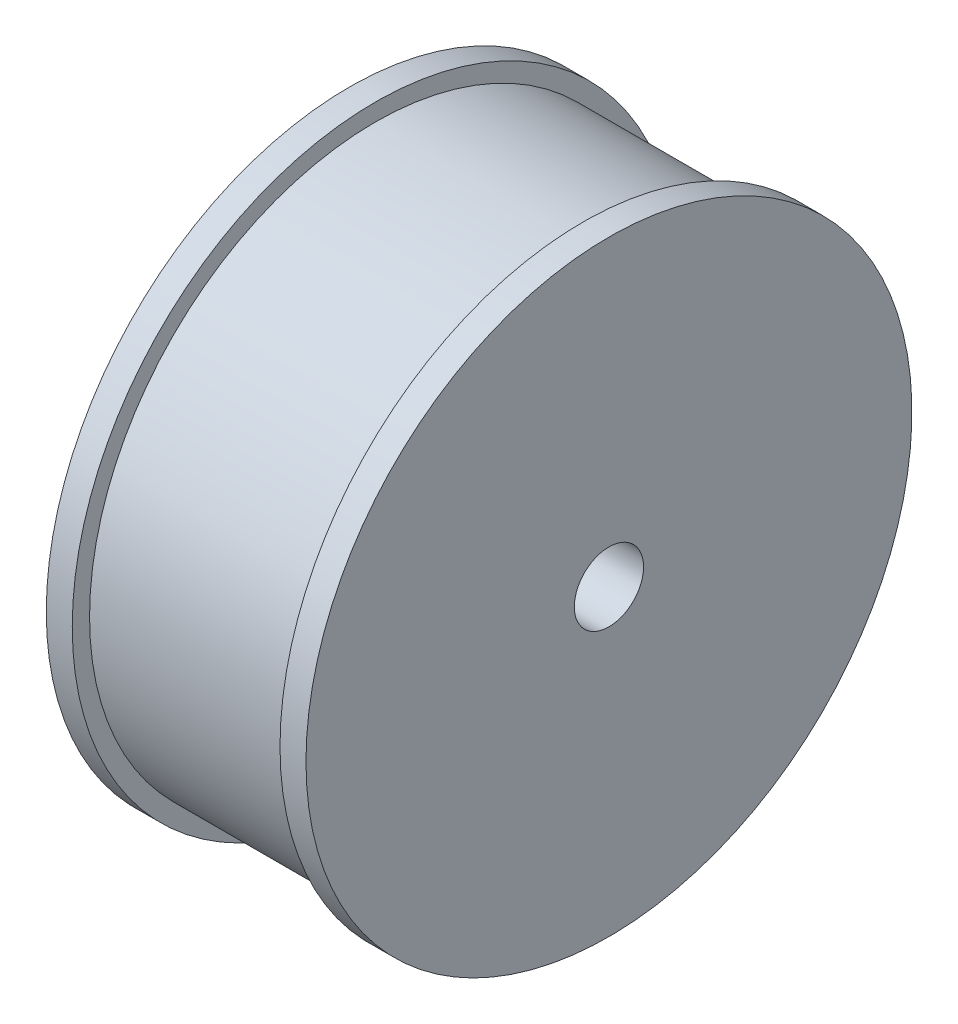
SolidWorks part; units mm, degrees
ref_plane "Front" through (0, 0, 0) normal (0, 0, 1) x (1, 0, 0)
ref_plane "Top" through (0, 0, 0) normal (0, 1, 0) x (1, 0, 0)
ref_plane "Right" through (0, 0, 0) normal (1, 0, 0) x (0, 0, -1)
sketch "Sketch1" plane through (0, 0, 0) normal (0, 0, 1) x (1, 0, 0)
  line L1 (-15, 0) -> (15, 0) construction
  line L2 (12, 35) -> (15, 35)
  line L3 (15, 0) -> (15, 35)
  line L6 (12, 35) -> (12, 33)
  line L7 (-12, 33) -> (12, 33)
  line L8 (0, -50) -> (0, 50) construction
  line L9 (-15, 0) -> (-15, 35)
  line L10 (-12, 35) -> (-15, 35)
  line L11 (-12, 35) -> (-12, 33)
  line L12 (-15, 0) -> (15, 0)
  point P6 (0, 0)
  point P9 (0, 0)
  dimension "D1" = 15
  dimension "D2" = 35
  dimension "D3" = 3
  dimension "D4" = 2
revolve "Revolve1" add sketch "Sketch1" angle 360 about L1
sketch "Sketch4" plane through (-15, 0, 0) normal (-1, 0, 0) x (0, 0, 1)
  circle A0 centre (0, 0) radius 10
  dimension "D1" = 20
extrude "Boss-Extrude2" add sketch "Sketch4" along normal blind 8
sketch "Sketch6" plane through (15, 0, 0) normal (1, 0, 0) x (0, 0, -1)
  circle A0 centre (0, 0) radius 4
  dimension "D1" = 8
extrude "Cut-Extrude1" cut sketch "Sketch6" against normal up to surface (38 mm away) up to face at (-23, 0, 10)
